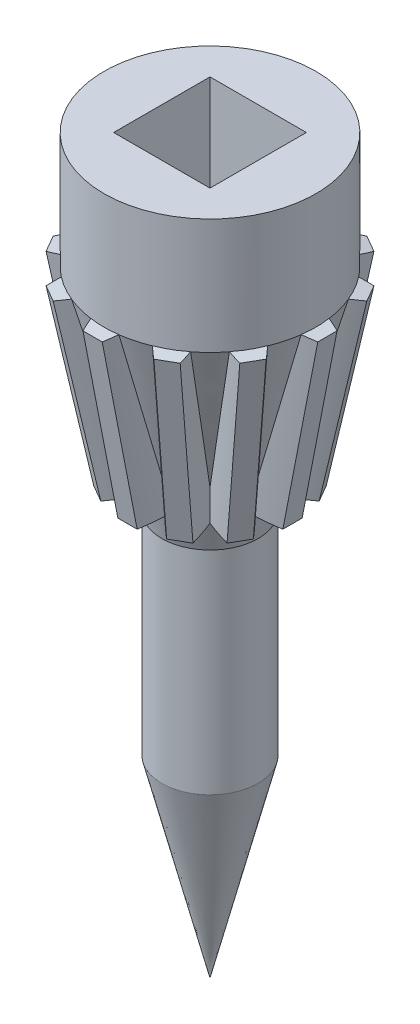
SolidWorks part; units mm, degrees
ref_plane "Front Plane" through (0, 0, 0) normal (0, 0, 1) x (1, 0, 0)
ref_plane "Top Plane" through (0, 0, 0) normal (0, 1, 0) x (1, 0, 0)
ref_plane "Right Plane" through (0, 0, 0) normal (1, 0, 0) x (0, 0, -1)
sketch "Sketch1" plane through (0, 0, 0) normal (0, 0, 1) x (1, 0, 0)
  line L0 (11, 44) -> (5, 22)
  line L1 (5, 0) -> (5, 22)
  line L2 (0, 56) -> (11, 56)
  line L3 (11, 56) -> (11, 44)
  line L5 (0, 56) -> (0, -20)
  line L6 (5, 0) -> (0, -20)
  dimension "D1" = 5
  dimension "D2" = 22
  dimension "D3" = 11
  dimension "D5" = 12
  dimension "D6" = 76
revolve "Revolve1" add sketch "Sketch1" angle 360 about L5
sketch "Sketch2" plane through (0, 56, 0) normal (0, 1, 0) x (1, 0, 0)
  line L1 (-5, -5) -> (5, -5)
  line L2 (-5, -5) -> (-5, 5)
  line L3 (-5, 5) -> (5, 5)
  line L4 (5, -5) -> (5, 5)
  line L5 (-5, -5) -> (5, 5) construction
  line L6 (-5, 5) -> (5, -5) construction
  point P0 (0, 0)
extrude "Cut-Extrude1" cut sketch "Sketch2" against normal blind 14
sketch "Sketch3" plane through (0, 0, 0) normal (0, 0, 1) x (1, 0, 0)
  line L0 (-11, 44) -> (-23.4739, 41.5753) construction
  line L1 (-11, 56) -> (-11, 44) construction
  line L2 (11, 56) -> (-11, 56) construction
  line L3 (-11, 44) -> (-34.756, 44) construction
  dimension "D1" = 12
  dimension "D2" = 11
ref_plane "Plane2" through (0, 0, 0) normal (0, 0, -1) x (-0.9816, -0.1908, 0)
ref_plane "Plane3" through (-8.6418, 44.4584, 0) normal (0.1908, -0.9816, 0) x (-0.9816, -0.1908, 0)
sketch "Sketch4" plane through (-8.6418, 44.4584, 0) normal (0.1908, -0.9816, 0) x (-0.9816, -0.1908, 0)
  line L0 (3.6126, -1) -> (3.6126, 1)
  line L2 (-21.4832, 0) -> (49000, 0) construction
  arc A0 (3.6126, 1) -> (-0.0672, 1.9989) centre (-2.939, -15.8583) ccw
  arc A1 (3.6126, -1) -> (-0.0672, -1.9989) centre (-2.939, 15.8583) cw
  ellipse E0 centre (-10.6853, 0) end of major axis (-10.6853, 11) minor radius 10.7979 construction
  ellipse E1 centre (-10.6853, 0) end of major axis (-10.6853, 11) minor radius 10.7979 (-0.0672, -1.9989) -> (-0.0672, 1.9989) ccw
  point P6 (3.6126, 0)
  dimension "D1" = 1
  dimension "D2" = 3.5
extrude "Boss-Extrude1" add sketch "Sketch4" along normal blind 19
pattern_circular "CirPattern1" count 12 over 360 about axis through (0, 0, 0) along (0, 1, 0) of "Boss-Extrude1"
